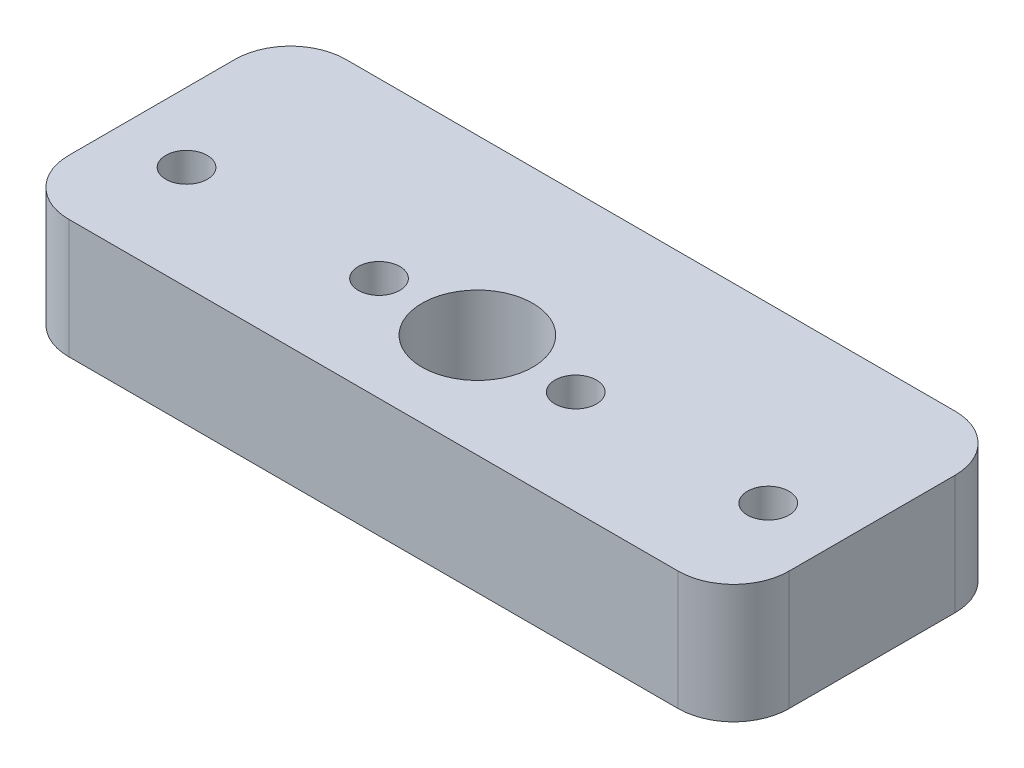
SolidWorks part; units mm, degrees
ref_plane "Front Plane" through (0, 0, 0) normal (0, 0, 1) x (1, 0, 0)
ref_plane "Top Plane" through (0, 0, 0) normal (0, 1, 0) x (1, 0, 0)
ref_plane "Right Plane" through (0, 0, 0) normal (1, 0, 0) x (0, 0, -1)
sketch "Sketch1" plane through (0, 0, 0) normal (0, 1, 0) x (1, 0, 0)
  line L0 (-26, -2.5) -> (26, -2.5) construction
  line L1 (-22, 10) -> (22, 10)
  line L2 (-26, 6) -> (-26, -6)
  line L3 (-22, -10) -> (22, -10)
  line L4 (26, 6) -> (26, -6)
  line L5 (-26, 10) -> (26, -10) construction
  line L6 (-26, -10) -> (26, 10) construction
  line L7 (0, -10) -> (0, 10) construction
  line L8 (26, 10) -> (-26, -10) construction
  arc A0 (-26, -6) -> (-22, -10) centre (-22, -6) ccw
  arc A1 (22, -10) -> (26, -6) centre (22, -6) ccw
  arc A2 (22, 10) -> (26, 6) centre (22, 6) cw
  arc A3 (-22, 10) -> (-26, 6) centre (-22, 6) ccw
  circle A4 centre (0, -2.5) radius 4
  circle A5 centre (7.1, -2.5) radius 1.5
  circle A6 centre (21, -2.5) radius 1.5
  circle A7 centre (-21, -2.5) radius 1.5
  circle A8 centre (-7.1, -2.5) radius 1.5
  point P0 (0, 0)
  dimension "D3" = 4
  dimension "D4" = 8
  dimension "D5" = 3
  dimension "D6" = 3
  dimension "D1" = 20
  dimension "D2" = 52
  dimension "D7" = 7.5
  dimension "D8" = 7.1
  dimension "D9" = 5
extrude "Boss-Extrude1" add sketch "Sketch1" along normal blind 8.6
